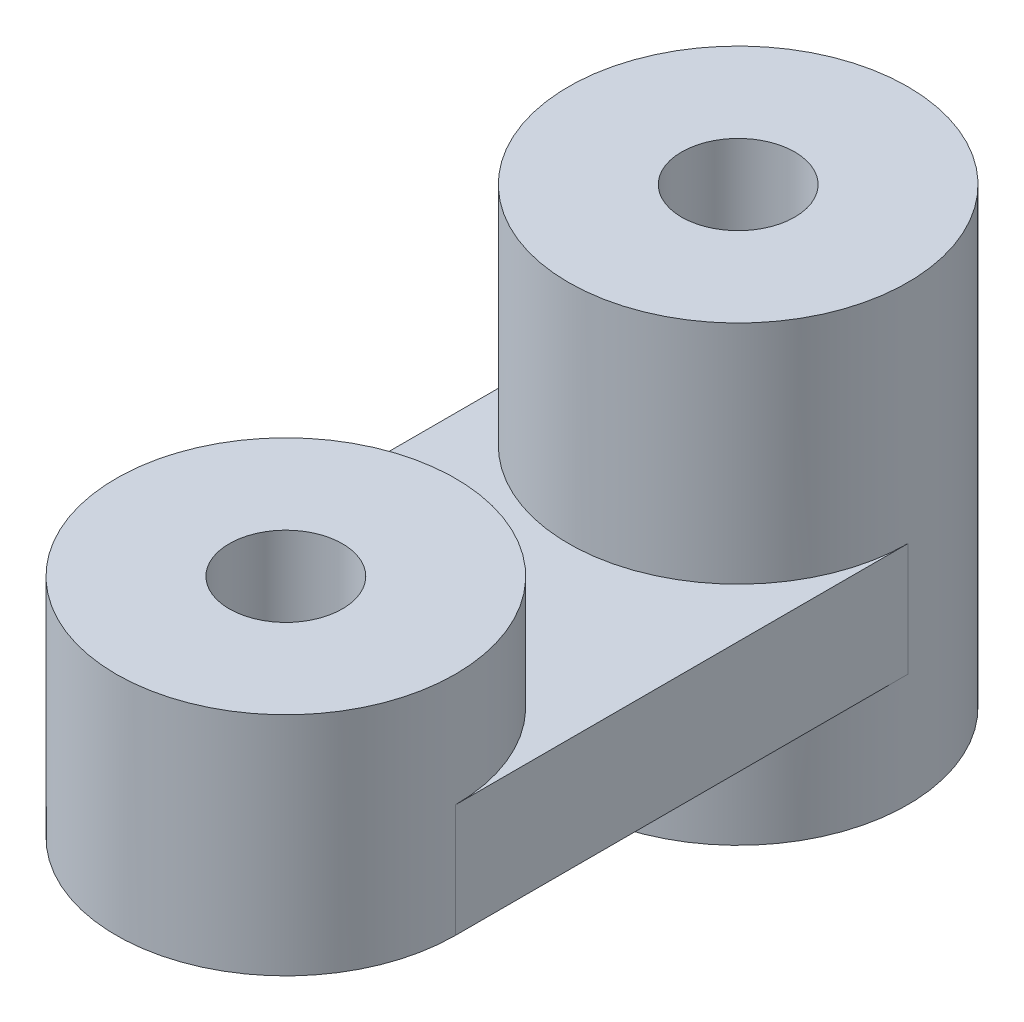
SolidWorks part; units mm, degrees
ref_plane "Alzado" through (0, 0, 0) normal (0, 0, 1) x (1, 0, 0)
ref_plane "Planta" through (0, 0, 0) normal (0, 1, 0) x (1, 0, 0)
ref_plane "Vista lateral" through (0, 0, 0) normal (1, 0, 0) x (0, 0, -1)
sketch "Croquis3" plane through (0, 0, 0) normal (0, 1, 0) x (1, 0, 0)
  line L1 (-7.5, -7.5) -> (-7.5, 12.5)
  line L2 (-7.5, 0) -> (7.5, 0) construction
  line L3 (7.5, -7.5) -> (7.5, 12.5)
  arc A0 (7.5, -7.5) -> (-7.5, -7.5) centre (0, -7.5) cw
  arc A1 (-7.5, 12.5) -> (7.5, 12.5) centre (0, 12.5) cw
  circle A2 centre (0, 12.5) radius 2.5
  circle A3 centre (0, -7.5) radius 2.5
  point P3 (7.5, 0)
  point P16 (0, 0)
  dimension "D4" = 5
  dimension "D1" = 7.5
  dimension "D2" = 15
  dimension "D3" = 12.5
extrude "Saliente-Extruir1" add sketch "Croquis3" along normal blind 5
sketch "Croquis4" plane through (0, 5, 0) normal (0, 1, 0) x (1, 0, 0)
  circle A0 centre (0, -7.5) radius 7.5
  arc A1 (-7.5, -7.5) -> (7.5, -7.5) centre (0, -7.5) ccw construction
  circle A2 centre (0, -7.5) radius 2.5 construction
  circle A3 centre (0, -7.5) radius 2.5
  point P3 (0, -7.5)
extrude "Saliente-Extruir2" add sketch "Croquis4" along normal blind 5
sketch "Croquis5" plane through (0, 5, 0) normal (0, 1, 0) x (1, 0, 0)
  circle A0 centre (0, 12.5) radius 7.5
  circle A1 centre (0, 12.5) radius 2.5 construction
  circle A2 centre (0, 12.5) radius 2.5
  arc A3 (7.5, 12.5) -> (-7.5, 12.5) centre (0, 12.5) ccw construction
extrude "Saliente-Extruir3" add sketch "Croquis5" along normal blind 10
sketch "Croquis7" plane through (0, 0, 0) normal (0, -1, 0) x (1, 0, 0)
  circle A0 centre (0, -12.5) radius 7.5
  circle A1 centre (0, -12.5) radius 2.5 construction
  circle A2 centre (0, -12.5) radius 2.5
  arc A3 (-7.5, -12.5) -> (7.5, -12.5) centre (0, -12.5) ccw construction
extrude "Saliente-Extruir4" add sketch "Croquis7" along normal blind 5
